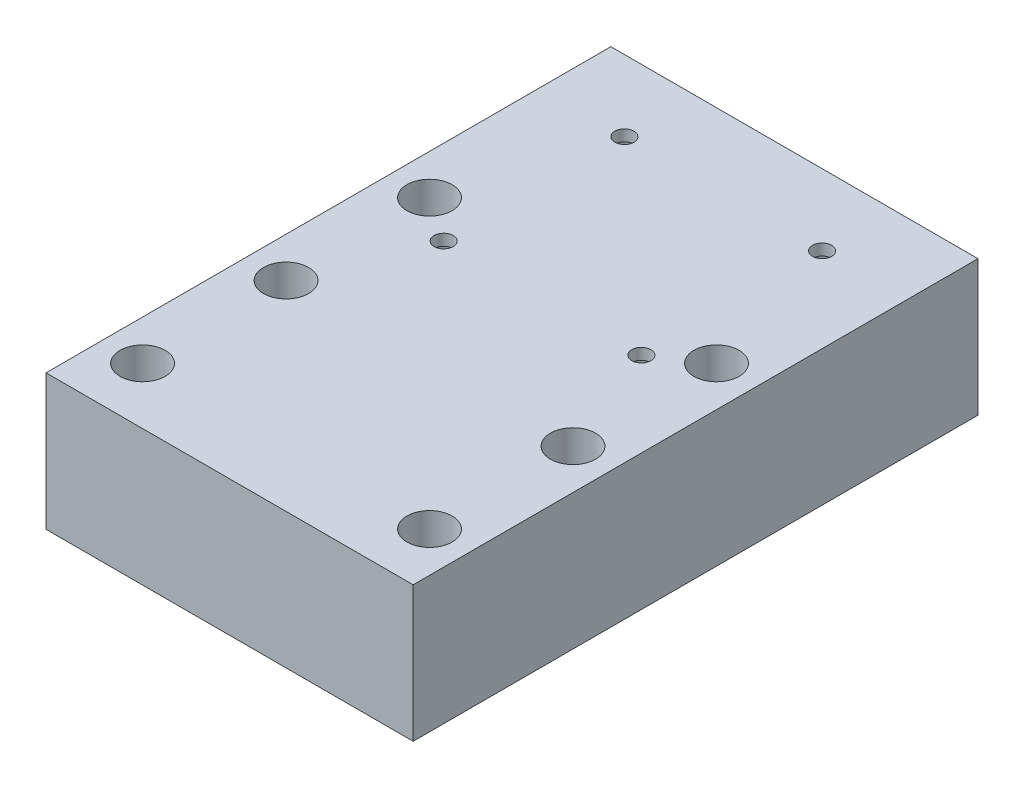
SolidWorks part; units mm, degrees
ref_plane "Front Plane" through (0, 0, 0) normal (0, 0, 1) x (1, 0, 0)
ref_plane "Top Plane" through (0, 0, 0) normal (0, 1, 0) x (1, 0, 0)
ref_plane "Right Plane" through (0, 0, 0) normal (1, 0, 0) x (0, 0, -1)
sketch "Sketch1" plane through (0, 0, 0) normal (0, 1, 0) x (1, 0, 0)
  line L0 (-25.4, -40) -> (25.4, -40) construction
  line L1 (-32.5, 50) -> (32.5, 50)
  line L2 (-32.5, 50) -> (-32.5, -50)
  line L3 (-32.5, -50) -> (32.5, -50)
  line L4 (32.5, 50) -> (32.5, -50)
  line L5 (-32.5, 50) -> (32.5, -50) construction
  line L6 (-32.5, -50) -> (32.5, 50) construction
  line L7 (0, -3.2164) -> (0, 21.8607) construction
  circle A0 centre (-25.4, -40) radius 4
  circle A1 centre (25.4, -40) radius 4
  circle A2 centre (25.4, -14.6) radius 4
  circle A3 centre (-25.4, -14.6) radius 4
  circle A4 centre (-17.5, 5.4) radius 1.7
  circle A5 centre (17.5, 37.4) radius 1.7
  circle A6 centre (-17.5, 37.4) radius 1.7
  circle A7 centre (17.5, 5.4) radius 1.7
  circle A8 centre (25.4, 10.8) radius 4
  circle A9 centre (-25.4, 10.8) radius 4
  point P0 (0, 0)
  dimension "D3" = 8
  dimension "D4" = 8
  dimension "D8" = 3.4
  dimension "D9" = 3.4
  dimension "D1" = 65
  dimension "D2" = 100
  dimension "D5" = 50.8
  dimension "D6" = 10
  dimension "D7" = 2
  dimension "D10" = 35
  dimension "D11" = 32
  dimension "D12" = 0
  dimension "D13" = 20
  dimension "D14" = 25.4
  dimension "D15" = 2
extrude "Boss-Extrude1" add sketch "Sketch1" along normal blind 24
sketch "Sketch3" plane through (0, 0, 0) normal (0, -1, 0) x (1, 0, 0)
  circle A0 centre (-17.5, -5.4) radius 3.5
  circle A1 centre (17.5, -5.4) radius 3.5
  circle A2 centre (-17.5, -37.4) radius 3.5
  circle A3 centre (17.5, -37.4) radius 3.5
  dimension "D1" = 7
  dimension "D2" = 7
  dimension "D3" = 7
  dimension "D4" = 7
extrude "Cut-Extrude1" cut sketch "Sketch3" against normal blind 22
